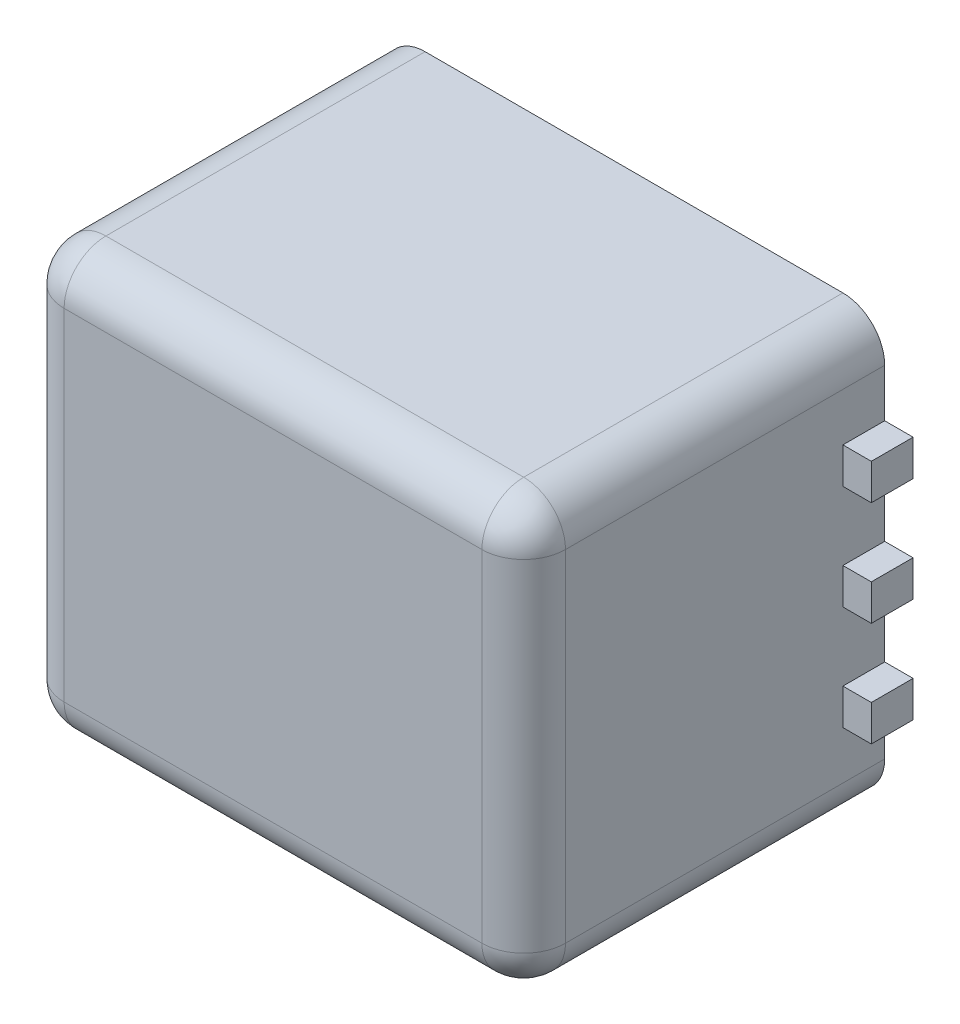
SolidWorks part; units mm, degrees
ref_plane "Front Plane" through (0, 0, 0) normal (0, 0, 1) x (1, 0, 0)
ref_plane "Top Plane" through (0, 0, 0) normal (0, 1, 0) x (1, 0, 0)
ref_plane "Right Plane" through (0, 0, 0) normal (1, 0, 0) x (0, 0, -1)
sketch "Sketch1" plane through (0, 0, 0) normal (0, 0, 1) x (1, 0, 0)
  line L1 (0, 0) -> (12, 0)
  line L2 (0, 0) -> (0, 10.16)
  line L3 (0, 10.16) -> (12, 10.16)
  line L4 (12, 0) -> (12, 10.16)
  dimension "D1" = 12
  dimension "D2" = 10.16
extrude "Boss-Extrude1" add sketch "Sketch1" along normal blind 8.64
fillet "Fillet1" radius 1 8 edges at (6, 10.16, 8.64) (12, 5.08, 8.64) (6, 0, 8.64) (0, 5.08, 8.64) (0, 0, 4.32) (12, 0, 4.32) (12, 10.16, 4.32) (0, 10.16, 4.32)
sketch "Sketch2" plane through (0, 0, 0) normal (0, 0, -1) x (-1, 0, 0)
  line L0 (-9.3206, 5.08) -> (-2.6794, 5.08) construction
  line L1 (-9.3206, 8.01) -> (-12.68, 8.01)
  line L2 (-9.3206, 8.01) -> (-9.3206, 7.15)
  line L3 (-9.3206, 7.15) -> (-12.68, 7.15)
  line L4 (-12.68, 8.01) -> (-12.68, 7.15)
  line L5 (-9.3206, 5.51) -> (-12.68, 5.51)
  line L6 (-9.3206, 5.51) -> (-9.3206, 4.65)
  line L7 (-9.3206, 4.65) -> (-12.68, 4.65)
  line L8 (-12.68, 5.51) -> (-12.68, 4.65)
  line L9 (-9.3206, 3.01) -> (-12.68, 3.01)
  line L10 (-9.3206, 3.01) -> (-9.3206, 2.15)
  line L11 (-9.3206, 2.15) -> (-12.68, 2.15)
  line L12 (-12.68, 3.01) -> (-12.68, 2.15)
  line L13 (-2.6794, 8.01) -> (0.68, 8.01)
  line L14 (-2.6794, 8.01) -> (-2.6794, 7.15)
  line L15 (-2.6794, 7.15) -> (0.68, 7.15)
  line L16 (0.68, 8.01) -> (0.68, 7.15)
  line L17 (-2.6794, 5.51) -> (0.68, 5.51)
  line L18 (-2.6794, 5.51) -> (-2.6794, 4.65)
  line L19 (-2.6794, 4.65) -> (0.68, 4.65)
  line L20 (0.68, 5.51) -> (0.68, 4.65)
  line L21 (-2.6794, 3.01) -> (0.68, 3.01)
  line L22 (-2.6794, 3.01) -> (-2.6794, 2.15)
  line L23 (-2.6794, 2.15) -> (0.68, 2.15)
  line L24 (0.68, 3.01) -> (0.68, 2.15)
  line L25 (-6, 10.16) -> (-6, 0) construction
  line L26 (-11, 10.16) -> (-1, 10.16) construction
  line L27 (-1, 0) -> (-11, 0) construction
  line L28 (-9.3206, 7.15) -> (-9.3206, 5.51) construction
  line L29 (-9.3206, 4.65) -> (-9.3206, 3.01) construction
  line L30 (-2.6794, 3.01) -> (-2.6794, 4.65) construction
  line L31 (-2.6794, 5.51) -> (-2.6794, 7.15) construction
  point P32 (-6, 5.08)
  point P33 (-6, 5.08)
  point P34 (0, 0)
  point P35 (-2.6794, 2.6187)
  dimension "D1" = 0.86
  dimension "D2" = 3.3594
  dimension "D3" = 13.36
  dimension "D4" = 2.5
extrude "Boss-Extrude2" add sketch "Sketch2" against normal blind 1
